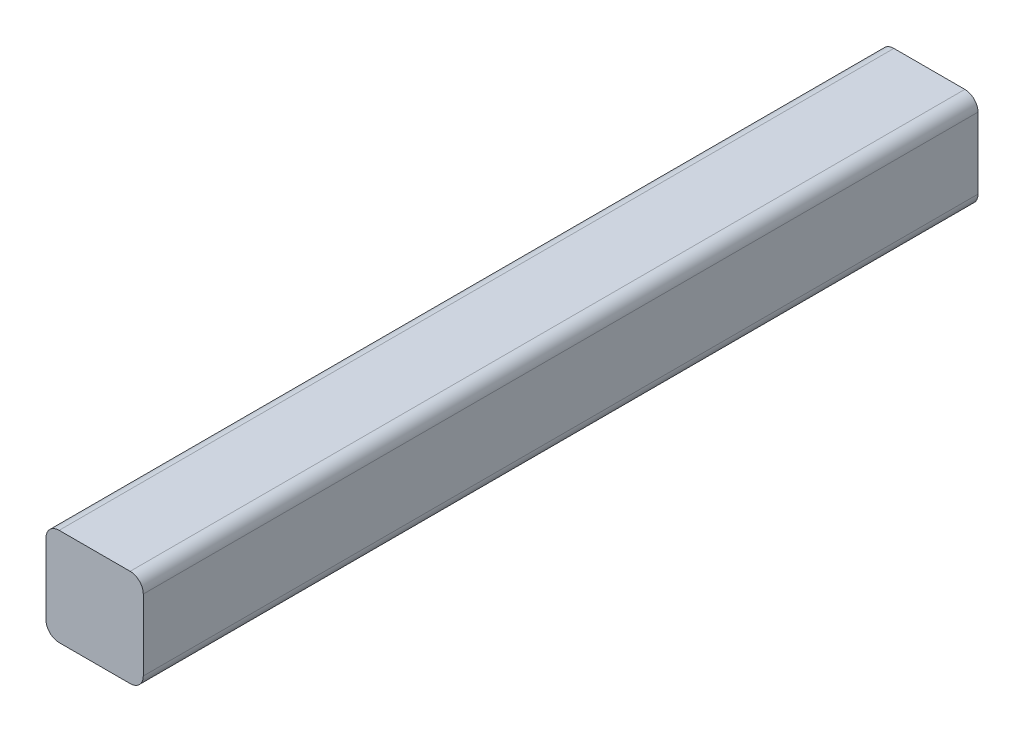
SolidWorks part; units mm, degrees
ref_plane "Front Plane" through (0, 0, 0) normal (0, 0, 1) x (1, 0, 0)
ref_plane "Top Plane" through (0, 0, 0) normal (0, 1, 0) x (1, 0, 0)
ref_plane "Right Plane" through (0, 0, 0) normal (1, 0, 0) x (0, 0, -1)
sketch "Sketch1" plane through (0, 0, 0) normal (0, 0, 1) x (1, 0, 0)
  line L1 (7.4, -7.4) -> (-7.4, -7.4)
  line L2 (7.4, -7.4) -> (7.4, 7.4)
  line L3 (7.4, 7.4) -> (-7.4, 7.4)
  line L4 (-7.4, -7.4) -> (-7.4, 7.4)
  line L5 (7.4, -7.4) -> (-7.4, 7.4) construction
  line L6 (7.4, 7.4) -> (-7.4, -7.4) construction
  point P0 (0, 0)
  dimension "D1" = 14.8
  dimension "D2" = 14.8
extrude "Boss-Extrude1" add sketch "Sketch1" along normal blind 127
fillet "Fillet1" radius 2 4 edges at (-7.4, -7.4, 63.5) (7.4, -7.4, 63.5) (-7.4, 7.4, 63.5) (7.4, 7.4, 63.5)
